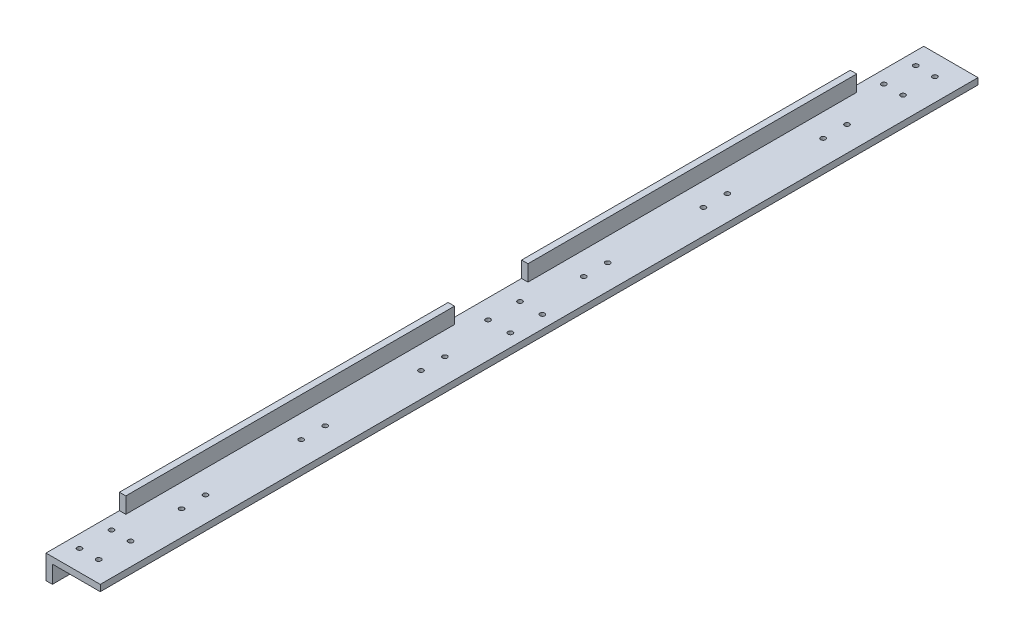
SolidWorks part; units mm, degrees
ref_plane "Front Plane" through (0, 0, 0) normal (0, 0, 1) x (1, 0, 0)
ref_plane "Top Plane" through (0, 0, 0) normal (0, 1, 0) x (1, 0, 0)
ref_plane "Right Plane" through (0, 0, 0) normal (1, 0, 0) x (0, 0, -1)
sketch "Sketch1" plane through (0, 0, 0) normal (0, 0, 1) x (1, 0, 0)
  line L1 (-2.1289, -13.3941) -> (1.8711, -13.3941)
  line L2 (1.8711, -13.3941) -> (1.8711, -2.3941)
  line L3 (1.8711, -2.3941) -> (31.8711, -2.3941)
  line L4 (31.8711, -2.3941) -> (31.8711, 1.6059)
  line L5 (31.8711, 1.6059) -> (1.8711, 1.6059)
  line L6 (1.8711, 1.6059) -> (1.8711, 11.6059)
  line L7 (1.8711, 11.6059) -> (-2.1289, 11.6059)
  line L8 (-2.1289, 11.6059) -> (-2.1289, -13.3941)
  dimension "D1" = 4
  dimension "D2" = 4
  dimension "D3" = 4
  dimension "D4" = 30
  dimension "D5" = 10
  dimension "D6" = 25
extrude "Boss-Extrude1" add sketch "Sketch1" along normal blind 550
sketch "Sketch2" plane through (-2.1289, 0, 0) normal (-1, 0, 0) x (0, 0, 1)
  line L0 (0, 11.6059) -> (0, 1.6059)
  line L1 (0, 11.6059) -> (0, -13.3941) construction
  line L2 (0, 1.6059) -> (46, 1.6059)
  line L3 (46, 1.6059) -> (46, 11.6059)
  line L4 (550, 11.6059) -> (0, 11.6059) construction
  line L5 (46, 11.6059) -> (0, 11.6059)
  dimension "D2" = 46
extrude "Cut-Extrude1" cut sketch "Sketch2" against normal through all
sketch "Sketch3" plane through (-2.1289, 0, 0) normal (-1, 0, 0) x (0, 0, 1)
  line L0 (275, -13.3941) -> (275, 11.6059) construction
  line L1 (550, -13.3941) -> (0, -13.3941) construction
  line L2 (550, 11.6059) -> (46, 11.6059) construction
  line L3 (0, 1.6059) -> (46, 1.6059) construction
  line L4 (252, 11.6059) -> (298, 11.6059)
  line L5 (252, 11.6059) -> (252, 1.6059)
  line L6 (252, 1.6059) -> (298, 1.6059)
  line L7 (298, 11.6059) -> (298, 1.6059)
  dimension "D1" = 23
extrude "Cut-Extrude2" cut sketch "Sketch3" against normal through all
hole_wizard "Ø3.0mm Dowel Hole1" positions "Sketch7" profile "Sketch6" hole size "Ø3.0" standard "ISO"
sketch "Sketch7" plane through (0, 1.6059, 0) normal (0, 1, 0) x (1, 0, 0)
  line L0 (31.8711, -550) -> (31.8711, 0) construction
  line L1 (31.8711, 0) -> (-2.1289, 0) construction
  point P0 (17.8711, -13)
  point P2 (5.8711, -13)
  point P4 (5.8711, -33)
  point P6 (17.8711, -33)
  dimension "D1" = 4
  dimension "D2" = 14
  dimension "D3" = 20
  dimension "D4" = 13
sketch "Sketch6" plane through (17.8711, 1.6059, 13) normal (1, 0, 0) x (0, 0, 1)
  line L0 (0, 0) -> (0, 15.9013)
  line L1 (0, 15.9013) -> (1.5, 15)
  line L2 (1.5, 15) -> (1.5, 0)
  line L5 (1.5, 0) -> (0, 0)
  line L10 (0, 15.9013) -> (-1.5, 15) construction
  line L11 (0, -6.35) -> (0, 107.95) construction
  dimension "Hole Dia." = 3
  dimension "Hole Depth" = 15
  dimension "Drill Angle" = 118
sketch "Sketch8" plane through (-2.1289, 0, 0) normal (-1, 0, 0) x (0, 0, 1)
  line L0 (275, 1.6059) -> (275, -13.3941) construction
  line L1 (252, 1.6059) -> (298, 1.6059) construction
  line L2 (550, -13.3941) -> (0, -13.3941) construction
sketch "Sketch9" plane through (0, 1.6059, 0) normal (0, 1, 0) x (1, 0, 0)
  line L0 (-2.1289, -275) -> (31.8711, -275) construction
  line L1 (-2.1289, -252) -> (-2.1289, -298) construction
  line L2 (31.8711, -550) -> (31.8711, 0) construction
ref_plane "Plane1" through (0, 0, 275) normal (0, 0, 1) x (1, 0, 0)
mirror "Mirror2" about plane through (0, 0, 275) normal (0, 0, 1) of "Cut-Extrude1", "Ø3.0mm Dowel Hole1"
hole_wizard "Ø3.0mm Dowel Hole2" positions "Sketch11" profile "Sketch10" hole size "Ø3.0" standard "ISO"
sketch "Sketch11" plane through (0, 1.6059, 0) normal (0, 1, 0) x (1, 0, 0)
  line L0 (31.8711, -550) -> (31.8711, 0) construction
  line L1 (-18.7, -275) -> (18.7, -275) construction
  point P0 (23.8711, -285)
  point P2 (9.8711, -285)
  dimension "D1" = 8
  dimension "D2" = 10
  dimension "D3" = 14
sketch "Sketch10" plane through (23.8711, 1.6059, 285) normal (1, 0, 0) x (0, 0, 1)
  line L0 (0, 0) -> (0, 15.9013)
  line L1 (0, 15.9013) -> (1.5, 15)
  line L2 (1.5, 15) -> (1.5, 0)
  line L5 (1.5, 0) -> (0, 0)
  line L10 (0, 15.9013) -> (-1.5, 15) construction
  line L11 (0, -6.35) -> (0, 107.95) construction
  dimension "Hole Dia." = 3
  dimension "Hole Depth" = 15
  dimension "Drill Angle" = 118
mirror "Mirror3" about plane through (0, 0, 275) normal (0, 0, 1) of "Ø3.0mm Dowel Hole2"
hole_wizard "Ø3.0mm Dowel Hole3" positions "Sketch15" profile "Sketch14" hole size "Ø3.0" standard "ISO"
sketch "Sketch15" plane through (0, 1.6059, 0) normal (0, 1, 0) x (1, 0, 0)
  point P0 (16.2968, -231.5)
  point P2 (16.2968, -216.5)
  point P4 (16.2968, -156.5)
  point P6 (16.2968, -141.5)
  point P8 (16.2968, -81.5)
  point P10 (16.2968, -66.5)
  dimension "D1" = 15
  dimension "D2" = 15
  dimension "D3" = 15
  dimension "D4" = 60
  dimension "D5" = 60
  dimension "D6" = 20.5
sketch "Sketch14" plane through (16.2968, 1.6059, 231.5) normal (1, 0, 0) x (0, 0, 1)
  line L0 (0, 0) -> (0, 15.9013)
  line L1 (0, 15.9013) -> (1.5, 15)
  line L2 (1.5, 15) -> (1.5, 0)
  line L5 (1.5, 0) -> (0, 0)
  line L10 (0, 15.9013) -> (-1.5, 15) construction
  line L11 (0, -6.35) -> (0, 107.95) construction
  dimension "Hole Dia." = 3
  dimension "Hole Depth" = 15
  dimension "Drill Angle" = 118
mirror "Mirror4" about plane through (0, 0, 275) normal (0, 0, 1) of "Ø3.0mm Dowel Hole3"
